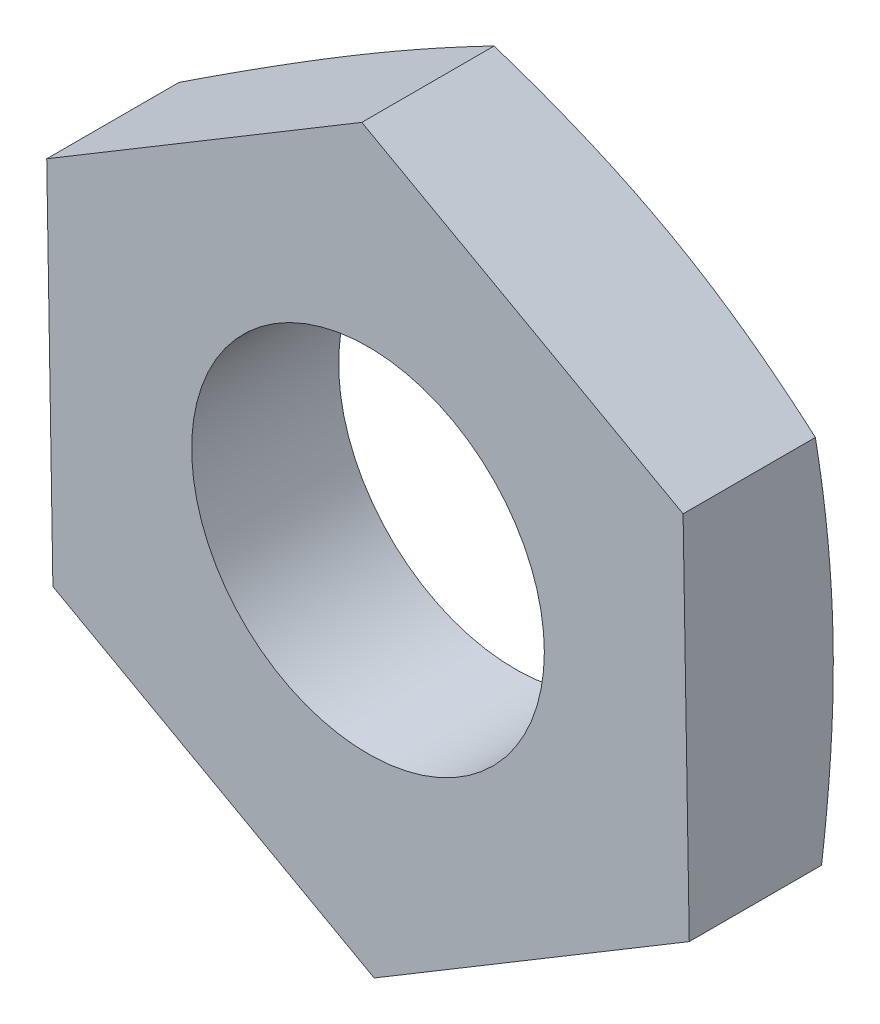
SolidWorks part; units mm, degrees
ref_plane "Front Plane" through (0, 0, 0) normal (0, 0, 1) x (1, 0, 0)
ref_plane "Top Plane" through (0, 0, 0) normal (0, 1, 0) x (1, 0, 0)
ref_plane "Right Plane" through (0, 0, 0) normal (1, 0, 0) x (0, 0, -1)
sketch "Sketch1" plane through (0, 0, 0) normal (0, 0, 1) x (1, 0, 0)
  line L1 (-12.8852, 7.4064) -> (-1.9548, 1.3386)
  line L2 (-1.9548, 1.3386) -> (8.7654, 7.7707)
  line L3 (8.7654, 7.7707) -> (8.5551, 20.2707)
  line L4 (8.5551, 20.2707) -> (-2.3753, 26.3386)
  line L5 (-2.3753, 26.3386) -> (-13.0955, 19.9064)
  line L6 (-13.0955, 19.9064) -> (-12.8852, 7.4064)
  circle A0 centre (-2.1651, 13.8386) radius 10.8268 construction
  circle A1 centre (-2.1651, 13.8386) radius 6
  dimension "D2" = 12
  dimension "D1" = 12.5
extrude "Boss-Extrude1" add sketch "Sketch1" along normal blind 5
ref_plane "Plane1" through (5.3634, 9.6614, 0) normal (0.4854, 0.8743, 0) x (0.8743, -0.4854, 0)
sketch "Sketch4" plane through (5.3634, 9.6614, 0) normal (0.4854, 0.8743, 0) x (0.8743, -0.4854, 0)
  line L0 (-8.6097, 0) -> (-8.6097, -5) construction
  line L1 (-2.3588, 0) -> (-14.8605, 0) construction
  line L2 (-2.3588, -5) -> (-14.8605, -5) construction
  line L3 (-19.4347, 0) -> (-21.1114, -0.5)
  line L4 (-14.8605, 0) -> (-21.1114, 0) construction
  line L5 (-21.1114, -5) -> (-21.1114, 0) construction
  line L6 (-21.1114, -0.5) -> (-21.5486, -0.5)
  line L7 (-21.5486, -0.5) -> (-21.5486, 0.4959)
  line L8 (-21.5486, 0.4959) -> (-19.4347, 0.4959)
  line L9 (-19.4347, 0.4959) -> (-19.4347, 0)
  dimension "D1" = 10.825
  dimension "D2" = 0.5
revolve "Cut-Revolve2" cut sketch "Sketch4" angle 360 about L0
